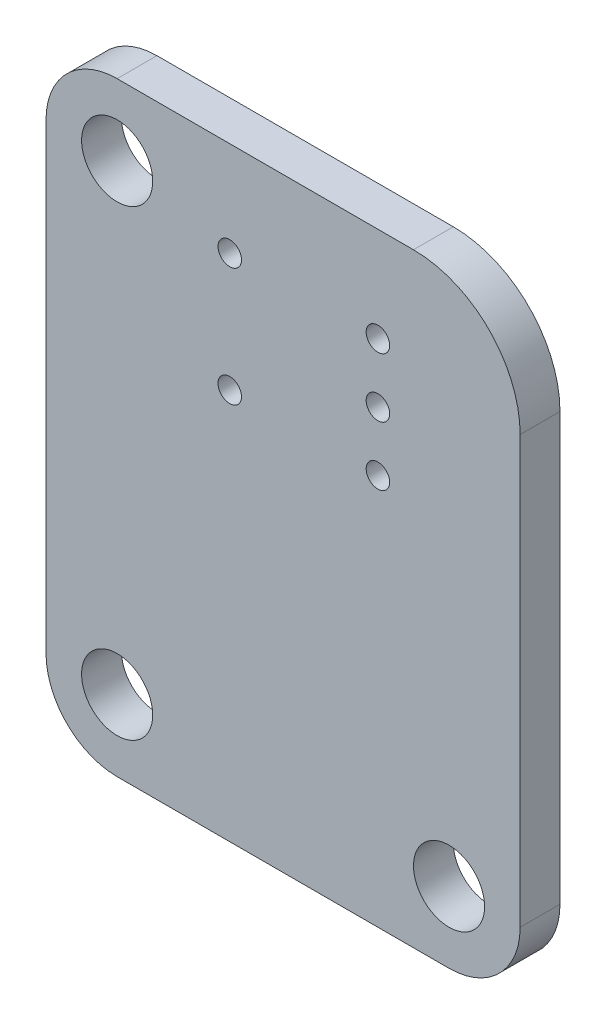
SolidWorks part; units mm, degrees
ref_plane "Front Plane" through (0, 0, 0) normal (0, 0, 1) x (1, 0, 0)
ref_plane "Top Plane" through (0, 0, 0) normal (0, 1, 0) x (1, 0, 0)
ref_plane "Right Plane" through (0, 0, 0) normal (1, 0, 0) x (0, 0, -1)
sketch "Sketch1" plane through (0, 0, -4.7) normal (0, 0, 1) x (1, 0, 0)
  line L0 (82.5, 65) -> (4.5, 65) construction
  line L1 (100, 26.864) -> (100, 37.5) construction
  line L2 (100, 42.5) -> (100, 60.5)
  line L3 (95.5, 65) -> (83, 65)
  line L4 (97, 39.5) -> (83, 39.5)
  line L5 (80, 42.5) -> (80, 62)
  arc A0 (100.5, 60.5) -> (95.5, 65.5) centre (95.5, 60.5) ccw construction
  arc A1 (83, 45.5) -> (83, 39.5) centre (83, 42.5) ccw construction
  arc A3 (100, 60.5) -> (95.5, 65) centre (95.5, 60.5) ccw
  arc A4 (83, 65) -> (80, 62) centre (83, 62) ccw
  arc A6 (83, 39.5) -> (80, 42.5) centre (83, 42.5) cw
  arc A7 (97, 39.5) -> (100, 42.5) centre (97, 42.5) ccw
  arc A18 (83, 59) -> (85.9468, 61.4375) centre (83, 62) ccw construction
  arc A19 (83, 59) -> (85.9468, 61.4375) centre (83, 62) ccw construction
extrude "BOARD" add sketch "Sketch1" along normal blind 1.68 separate body
sketch "Sketch2" plane through (0, 0, 0) normal (0, 0, 1) x (1, 0, 0)
  circle A0 centre (83, 42.5) radius 1.5
  circle A1 centre (97, 42.5) radius 1.5
  circle A2 centre (97, 35.5) radius 1.5
  circle A6 centre (83, 62) radius 1.5
  circle A7 centre (87.75, 56) radius 0.4953
  circle A8 centre (87.75, 61) radius 0.4953
  circle A9 centre (94, 58.5) radius 0.4953
  circle A10 centre (94, 56) radius 0.4953
  circle A11 centre (94, 61) radius 0.4953
  dimension "D1" = 3
extrude "PLATED HOLES" cut sketch "Sketch2" against normal through all
ref_plane "Plane1" through (0, 0, 0.8992) normal (0, 0, 1) x (1, 0, 0)
sketch "Sketch3" plane through (0, 0, 0) normal (0, 0, 1) x (1, 0, 0)
  line L0 (85.6, 63.45) -> (100.1, 63.45)
  line L1 (100.1, 63.45) -> (100.1, 53.55)
  line L2 (100.1, 53.55) -> (85.6, 53.55)
  line L3 (85.6, 53.55) -> (85.6, 63.45)
extrude "ENCODER_PEC09-2320F-S0015-1" [suppressed] add sketch "Sketch3" against normal blind 0.0254 separate body
sketch "Sketch4" plane through (0, 0, -3.02) normal (0, 0, 1) x (1, 0, 0)
  line L1 (86.2, 62) -> (99.5, 62)
  line L2 (86.2, 62) -> (86.2, 52.3)
  line L3 (86.2, 52.3) -> (99.5, 52.3)
  line L4 (99.5, 62) -> (99.5, 52.3)
  line L5 (87.2, 51.3) -> (93.2, 51.3)
  line L6 (87.2, 51.3) -> (87.2, 43.3)
  line L7 (87.2, 43.3) -> (93.2, 43.3)
  line L8 (93.2, 51.3) -> (93.2, 43.3)
sketch "Sketch5" plane through (0, 0, -3.02) normal (0, 0, 1) x (1, 0, 0)
  line L0 (1.0747, 0) -> (0, 0)
  line L1 (0, 0) -> (0, 1.0747)
  line L2 (0, 1.0747) -> (1.0747, 0)
  line L3 (80, 62) -> (80, 42.5) construction
  line L4 (83, 39.5) -> (97, 39.5) construction
  line L5 (81.524, 47.12) -> (81.524, 49.66) construction
  line L6 (81.524, 49.66) -> (81.524, 52.2) construction
  line L7 (81.524, 52.2) -> (81.524, 54.74) construction
  line L8 (81.524, 54.74) -> (81.524, 57.28) construction
  circle A0 centre (81.524, 47.12) radius 0.889
  circle A1 centre (81.524, 49.66) radius 0.889
  circle A2 centre (81.524, 52.2) radius 0.889
  circle A3 centre (81.524, 54.74) radius 0.889
  circle A4 centre (81.524, 57.28) radius 0.889
  dimension "D3" = 1.778
  dimension "D1" = 1.524
  dimension "D2" = 7.62
  dimension "D4" = 2.54
